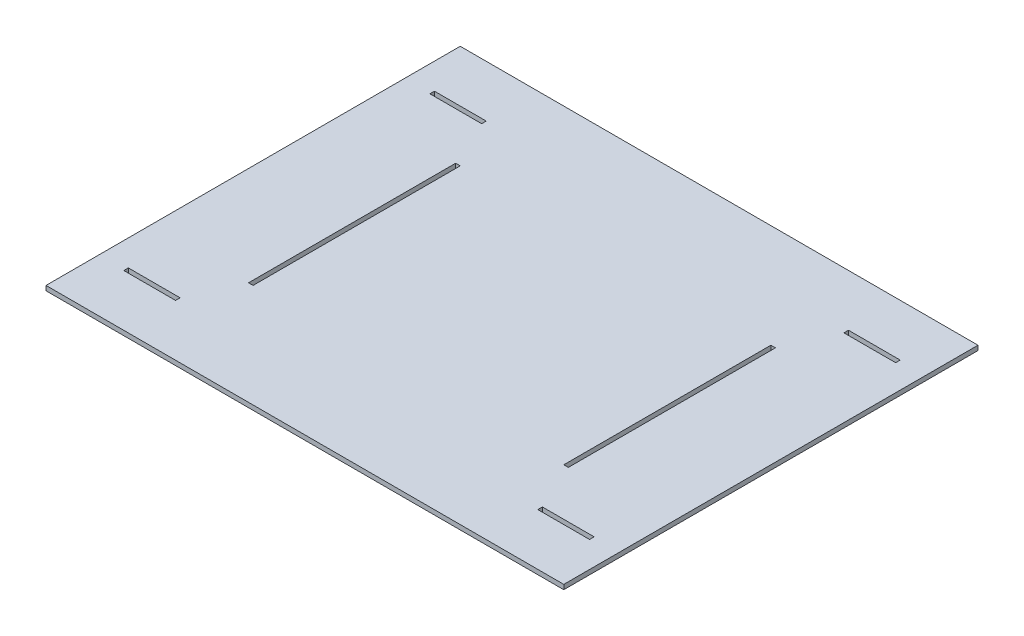
SolidWorks part; units mm, degrees
ref_plane "Front Plane" through (0, 0, 0) normal (0, 0, 1) x (1, 0, 0)
ref_plane "Top Plane" through (0, 0, 0) normal (0, 1, 0) x (1, 0, 0)
ref_plane "Right Plane" through (0, 0, 0) normal (1, 0, 0) x (0, 0, -1)
sketch "Sketch1" plane through (0, 0, 0) normal (0, 1, 0) x (1, 0, 0)
  line L1 (-250, 200) -> (250, 200)
  line L2 (-250, 200) -> (-250, -200)
  line L3 (-250, -200) -> (250, -200)
  line L4 (250, 200) -> (250, -200)
  line L5 (-250, 200) -> (250, -200) construction
  line L6 (-250, -200) -> (250, 200) construction
  point P0 (0, 0)
  dimension "D1" = 500
  dimension "D2" = 400
extrude "Boss-Extrude1" add sketch "Sketch1" along normal blind 4.5 contours L2 L3 L4 L1
sketch "Sketch2" plane through (0, 4.5, 0) normal (0, 1, 0) x (1, 0, 0)
  line L0 (-55, 0) -> (55, 0) construction
  line L1 (-154.4, 100) -> (-150, 100)
  line L2 (-154.4, 100) -> (-154.4, -100)
  line L3 (-154.4, -100) -> (-150, -100)
  line L4 (-150, 100) -> (-150, -100)
  line L5 (-154.4, 100) -> (-150, -100) construction
  line L6 (-154.4, -100) -> (-150, 100) construction
  line L8 (0, -55) -> (0, 55) construction
  point P0 (-152.2, 0)
  dimension "D1" = 200
  dimension "D2" = 4.4
  dimension "D3" = 150
extrude "Cut-Extrude1" cut sketch "Sketch2" against normal up to surface (4.5 mm away) contours L4 L3 L2 L1 up to face at (0, 0, 0)
mirror "Mirror2" about plane through (0, 0, 0) normal (1, 0, 0) of "Cut-Extrude1"
sketch "Sketch5" plane through (0, 4.5, 0) normal (0, 1, 0) x (1, 0, 0)
  line L0 (-154.4, 100) -> (-154.4, -100) construction
  line L1 (-224.9, 150) -> (-174.9, 150)
  line L2 (-224.9, 150) -> (-224.9, 145.6)
  line L3 (-224.9, 145.6) -> (-174.9, 145.6)
  line L4 (-174.9, 150) -> (-174.9, 145.6)
  line L5 (-224.9, 150) -> (-174.9, 145.6) construction
  line L6 (-224.9, 145.6) -> (-174.9, 150) construction
  line L7 (-250, 200) -> (250, 200) construction
  point P0 (-199.9, 147.8)
  dimension "D1" = 4.4
  dimension "D2" = 50
  dimension "D3" = 20.5
  dimension "D4" = 50
extrude "Cut-Extrude2" cut sketch "Sketch5" against normal up to surface (4.5 mm away) up to face at (152.2, 0, 0)
mirror "Mirror5" about plane through (0, 0, 0) normal (0, 0, 1) of "Cut-Extrude2" second plane through (0, 0, 0) second plane normal (1, 0, 0)
